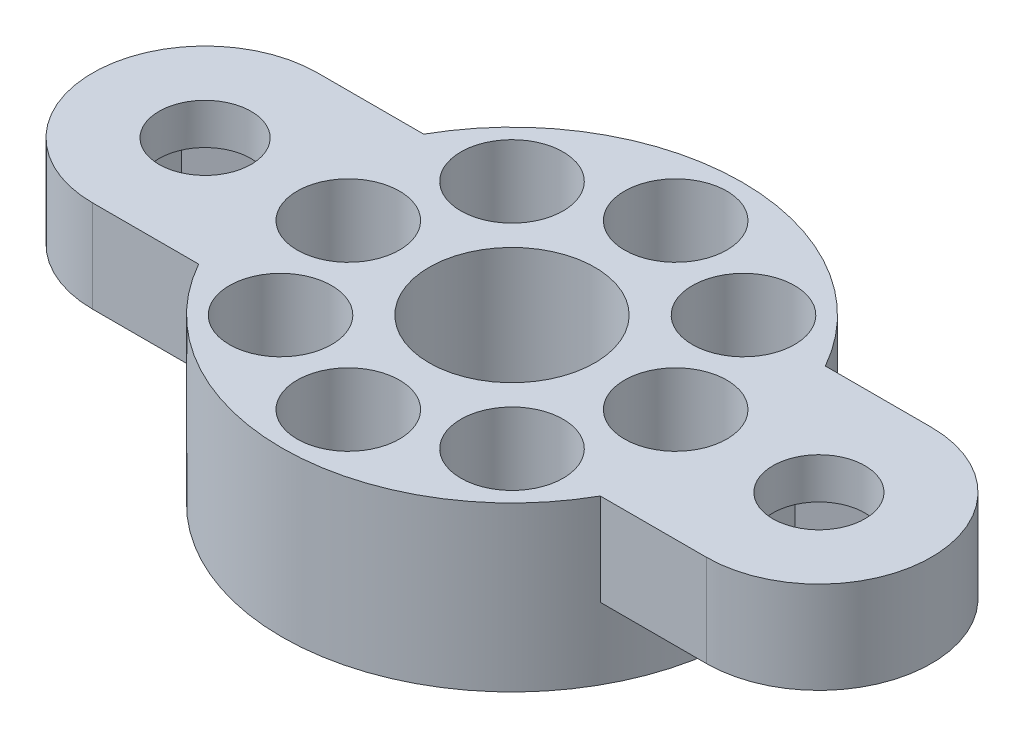
SolidWorks part; units mm, degrees
ref_plane "Front Plane" through (0, 0, 0) normal (0, 0, 1) x (1, 0, 0)
ref_plane "Top Plane" through (0, 0, 0) normal (0, 1, 0) x (1, 0, 0)
ref_plane "Right Plane" through (0, 0, 0) normal (1, 0, 0) x (0, 0, -1)
sketch "Sketch1" plane through (0, 0, 0) normal (0, 1, 0) x (1, 0, 0)
  circle A0 centre (0, 0) radius 11.25
  circle A1 centre (0, 8) radius 1.1
  circle A2 centre (5.6569, 5.6569) radius 1.1
  circle A3 centre (8, 0) radius 1.1
  circle A4 centre (5.6569, -5.6569) radius 1.1
  circle A5 centre (0, -8) radius 1.1
  circle A6 centre (-5.6569, -5.6569) radius 1.1
  circle A7 centre (-8, 0) radius 1.1
  circle A8 centre (-5.6569, 5.6569) radius 1.1
  circle A9 centre (0, 0) radius 4.05
  point P21 (0, 0)
  dimension "D1" = 22.5
  dimension "D2" = 2.2
  dimension "D5" = 8.1
  dimension "D3" = 8
  dimension "D4" = 8
extrude "Boss-Extrude1" add sketch "Sketch1" along normal blind 8
sketch "Sketch2" plane through (0, 8, 0) normal (0, 1, 0) x (1, 0, 0)
  circle A0 centre (0, 8) radius 2.5
  circle A1 centre (5.6569, 5.6569) radius 2.5
  circle A2 centre (8, 0) radius 2.5
  circle A3 centre (5.6569, -5.6569) radius 2.5
  circle A4 centre (0, -8) radius 2.5
  circle A5 centre (-5.6569, -5.6569) radius 2.5
  circle A6 centre (-8, 0) radius 2.5
  circle A7 centre (-5.6569, 5.6569) radius 2.5
  point P19 (0, 0)
  dimension "D1" = 5
  dimension "D2" = 8
extrude "Cut-Extrude1" cut sketch "Sketch2" against normal blind 6
sketch "Sketch3" plane through (0, 8, 0) normal (0, 1, 0) x (1, 0, 0)
  line L0 (-15, 0) -> (15, 0) construction
  line L1 (-15, 5.5) -> (-9.8139, 5.5)
  line L2 (-15, -5.5) -> (-9.8139, -5.5)
  line L3 (9.8139, 5.5) -> (15, 5.5)
  line L4 (9.8139, -5.5) -> (15, -5.5)
  arc A0 (-15, 5.5) -> (-15, -5.5) centre (-15, 0) ccw
  arc A1 (15, -5.5) -> (15, 5.5) centre (15, 0) ccw
  circle A2 centre (-15, 0) radius 2.25
  circle A3 centre (15, 0) radius 2.25
  arc A4 (-9.8139, 5.5) -> (-9.8139, -5.5) centre (0, 0) ccw
  arc A5 (9.8139, -5.5) -> (9.8139, 5.5) centre (0, 0) ccw
  point P2 (0, 0)
  dimension "D2" = 5.5
  dimension "D3" = 4.5
  dimension "D4" = 4.5
  dimension "D1" = 30
extrude "Boss-Extrude2" add sketch "Sketch3" against normal blind 4.5
sketch "Sketch4" plane through (0, 3.5, 0) normal (0, -1, 0) x (1, 0, 0)
  line L0 (0, -4.4) -> (0, 4.4) construction
  line L1 (-15, 3.1754) -> (-17.75, 1.5877)
  line L2 (-17.75, 1.5877) -> (-17.75, -1.5877)
  line L3 (-17.75, -1.5877) -> (-15, -3.1754)
  line L4 (-15, -3.1754) -> (-12.25, -1.5877)
  line L5 (-12.25, -1.5877) -> (-12.25, 1.5877)
  line L6 (-12.25, 1.5877) -> (-15, 3.1754)
  line L7 (12.25, 1.5877) -> (15, 3.1754)
  line L8 (12.25, -1.5877) -> (12.25, 1.5877)
  line L9 (15, -3.1754) -> (12.25, -1.5877)
  line L10 (17.75, -1.5877) -> (15, -3.1754)
  line L11 (17.75, 1.5877) -> (17.75, -1.5877)
  line L12 (15, 3.1754) -> (17.75, 1.5877)
  circle A0 centre (-15, 0) radius 2.75 construction
  dimension "D1" = 5.5
extrude "Cut-Extrude2" cut sketch "Sketch4" against normal blind 2.5
